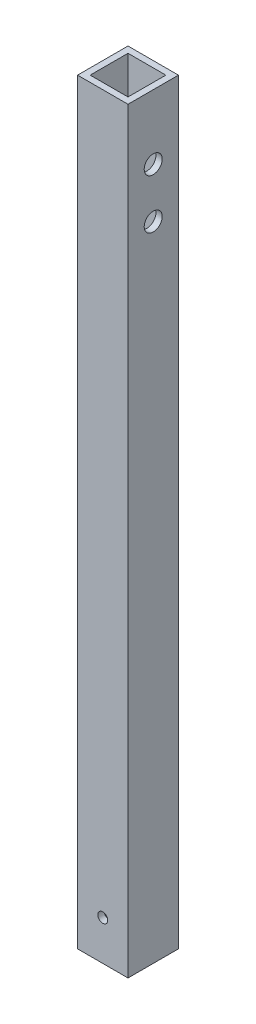
SolidWorks part; units mm, degrees
ref_plane "Front Plane" through (0, 0, 0) normal (0, 0, 1) x (1, 0, 0)
ref_plane "Top Plane" through (0, 0, 0) normal (0, 1, 0) x (1, 0, 0)
ref_plane "Right Plane" through (0, 0, 0) normal (1, 0, 0) x (0, 0, -1)
sketch "Sketch1" plane through (0, 0, 0) normal (0, 1, 0) x (1, 0, 0)
  line L0 (-9.525, 9.525) -> (-9.525, -9.525)
  line L1 (-12.7, 12.7) -> (12.7, 12.7)
  line L2 (-12.7, 12.7) -> (-12.7, -12.7)
  line L3 (-12.7, -12.7) -> (12.7, -12.7)
  line L4 (12.7, 12.7) -> (12.7, -12.7)
  line L5 (-12.7, 12.7) -> (12.7, -12.7) construction
  line L6 (-12.7, -12.7) -> (12.7, 12.7) construction
  line L7 (-9.525, -9.525) -> (9.525, -9.525)
  line L8 (9.525, 9.525) -> (9.525, -9.525)
  line L9 (-9.525, 9.525) -> (9.525, 9.525)
  point P0 (0, 0)
  dimension "D1" = 25.4
  dimension "D2" = 3.175
extrude "Boss-Extrude1" add sketch "Sketch1" along normal blind 381
sketch "Sketch2" plane through (0, 0, -12.7) normal (0, 0, -1) x (-1, 0, 0)
  circle A0 centre (0, 20) radius 2.5
  point P2 (0, 0)
  point P3 (0, 0)
  point P5 (0, 0)
  dimension "D1" = 5
  dimension "D2" = 20
extrude "Cut-Extrude1" cut sketch "Sketch2" against normal through all
sketch "Sketch3" plane through (-12.7, 0, 0) normal (-1, 0, 0) x (0, 0, 1)
  line L2 (-12.7, 381) -> (12.7, 381) construction
  circle A0 centre (0, 348.5) radius 4.5392
  circle A1 centre (0, 323.5) radius 4.5392
  point P4 (0, 0)
  point P5 (0, 0)
  point P6 (0, 0)
  point P9 (0, 0)
  point P10 (0, 381)
  dimension "D1" = 32.5
  dimension "D2" = 25
extrude "Cut-Extrude2" cut sketch "Sketch3" against normal through all
